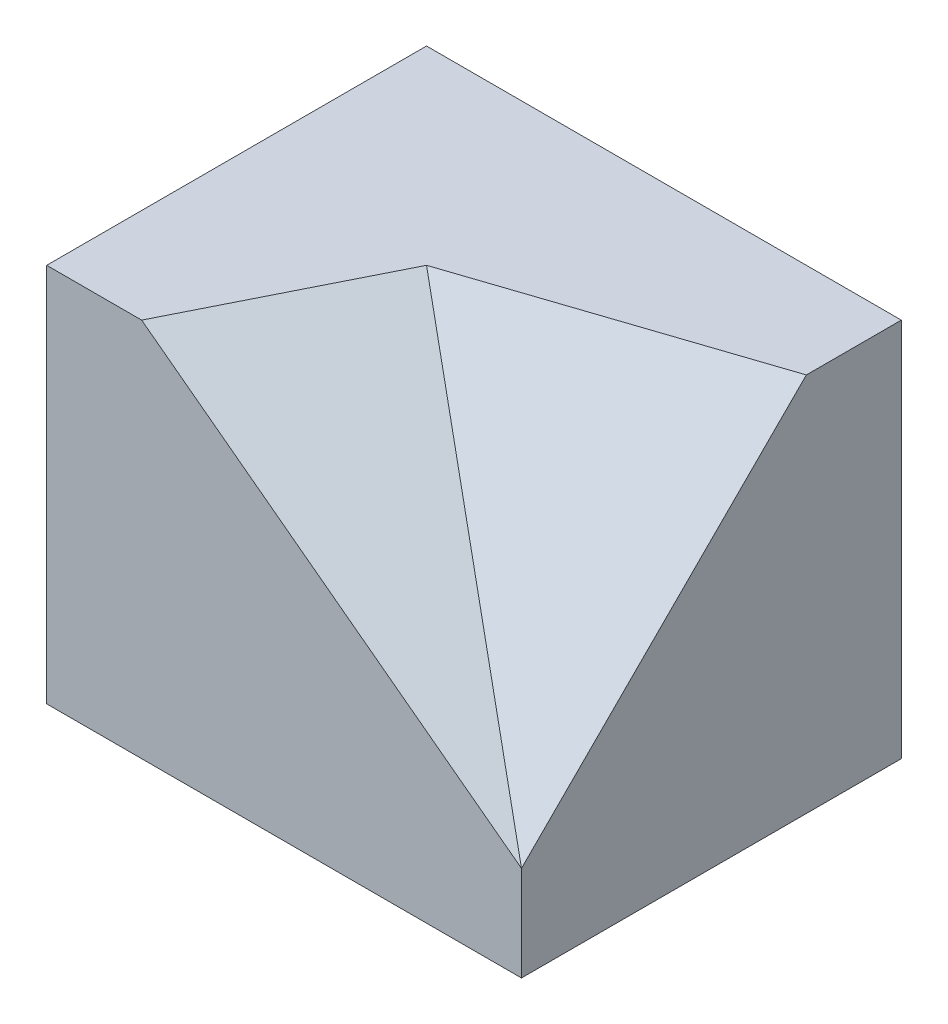
SolidWorks part; units mm, degrees
ref_plane "前基準面" through (0, 0, 0) normal (0, 0, 1) x (1, 0, 0)
ref_plane "上基準面" through (0, 0, 0) normal (0, 1, 0) x (1, 0, 0)
ref_plane "右基準面" through (0, 0, 0) normal (1, 0, 0) x (0, 0, -1)
sketch "草圖1" plane through (0, 0, 0) normal (0, 1, 0) x (1, 0, 0)
  line L1 (12.5, 10) -> (-12.5, 10)
  line L2 (12.5, 10) -> (12.5, -10)
  line L3 (12.5, -10) -> (-12.5, -10)
  line L4 (-12.5, 10) -> (-12.5, -10)
  line L5 (12.5, 10) -> (-12.5, -10) construction
  line L6 (12.5, -10) -> (-12.5, 10) construction
  point P0 (0, 0)
  dimension "D1" = 20
  dimension "D2" = 25
extrude "填料-伸長1" add sketch "草圖1" along normal blind 20
sketch "草圖2" plane through (0, 20, 0) normal (0, 1, 0) x (1, 0, 0)
  line L0 (12.5, -10) -> (-2.5, 0)
  line L1 (-2.5, 0) -> (-7.5, -10)
  line L2 (-12.5, -10) -> (12.5, -10) construction
  line L3 (-2.5, 0) -> (12.5, 5)
  line L4 (12.5, -10) -> (12.5, 10) construction
  dimension "D1" = 5
  dimension "D2" = 15
  dimension "D3" = 10
  dimension "D4" = 5
sketch "草圖3" plane through (0, 0, 10) normal (0, 0, 1) x (1, 0, 0)
  line L0 (-7.5, 20) -> (12.5, 5)
  line L1 (-12.5, 20) -> (12.5, 20) construction
  line L2 (-2.5, 20) -> (-7.5, 20) construction
  line L3 (12.5, 20) -> (12.5, 0) construction
  line L4 (12.5, 5) -> (-2.5, 20)
  dimension "D1" = 5
  dimension "D2" = 15
  dimension "D3" = 5
sketch "草圖4" plane through (12.5, 0, 0) normal (1, 0, 0) x (0, 0, -1)
  line L0 (0, 20) -> (-10, 5)
  line L1 (0, 20) -> (-10, 20) construction
  line L2 (0, 20) -> (5, 20) construction
  line L3 (-10, 20) -> (-10, 0) construction
  line L4 (-10, 5) -> (5, 20)
  line L5 (-10, 20) -> (10, 20) construction
  dimension "D1" = 5
ref_plane "平面2" through (7.9817, 10.6422, 3.9908) normal (-0.5747, -0.7663, -0.2873) x (-0.8184, 0.5381, 0.2018)
sketch "草圖5" plane through (7.9817, 10.6422, 3.9908) normal (-0.5747, -0.7663, -0.2873) x (-0.8184, 0.5381, 0.2018)
  line L2 (18.9177, -2.3408) -> (-5.5212, -7.6077) construction
  line L3 (12.808, 7.0225) -> (18.9177, -2.3408) construction
  line L6 (18.9177, -2.3408) -> (-5.5212, -7.6077)
  line L7 (12.808, 7.0225) -> (18.9177, -2.3408)
  line L8 (12.808, 7.0225) -> (-5.5212, -7.6077)
extrude "除料-伸長1" cut sketch "草圖5" against normal blind 20
ref_plane "平面3" through (3.0263, 9.0789, 9.0789) normal (0.2294, 0.6882, 0.6882) x (0.9733, -0.1622, -0.1622)
sketch "草圖7" plane through (3.0263, 9.0789, 9.0789) normal (0.2294, 0.6882, 0.6882) x (0.9733, -0.1622, -0.1622)
  line L0 (9.7333, -3.5355) -> (9.7333, 17.6777) construction
  line L1 (-5.6777, 14.1421) -> (9.7333, 17.6777) construction
  line L2 (9.7333, -3.5355) -> (9.7333, 17.6777)
  line L3 (-5.6777, 14.1421) -> (9.7333, 17.6777)
  line L4 (-5.6777, 14.1421) -> (9.7333, -3.5355)
extrude "除料-伸長5" cut sketch "草圖7" along normal blind 20
